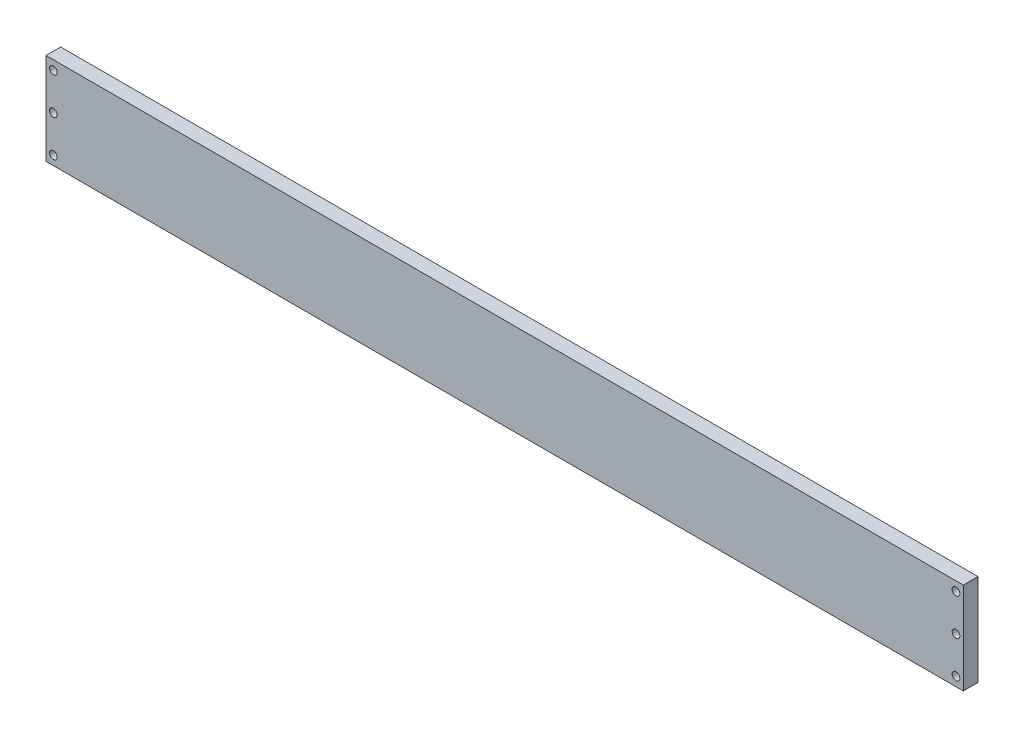
SolidWorks part; units mm, degrees
ref_plane "Front Plane" through (0, 0, 0) normal (0, 0, 1) x (1, 0, 0)
ref_plane "Top Plane" through (0, 0, 0) normal (0, 1, 0) x (1, 0, 0)
ref_plane "Right Plane" through (0, 0, 0) normal (1, 0, 0) x (0, 0, -1)
sketch "Sketch1" plane through (0, 0, 0) normal (0, 0, 1) x (1, 0, 0)
  line L0 (0, 25) -> (0, -25) construction
  line L1 (-250, 25) -> (250, 25)
  line L2 (-250, 25) -> (-250, -25)
  line L3 (-250, -25) -> (250, -25)
  line L4 (250, 25) -> (250, -25)
  line L5 (-250, 25) -> (250, -25) construction
  line L6 (-250, -25) -> (250, 25) construction
  line L7 (-246, 25) -> (-246, -25) construction
  circle A0 centre (-246, 0) radius 2.1
  circle A1 centre (-246, 20) radius 2.1
  circle A2 centre (-246, -20) radius 2.1
  circle A3 centre (246, 20) radius 2.1
  circle A4 centre (246, 0) radius 2.1
  circle A5 centre (246, -20) radius 2.1
  point P0 (0, 0)
  dimension "D3" = 4
  dimension "D4" = 5
  dimension "D1" = 500
  dimension "D2" = 50
  dimension "D5" = 5
extrude "Boss-Extrude1" add sketch "Sketch1" along normal blind 8 contours L1 L4 L3 L2
